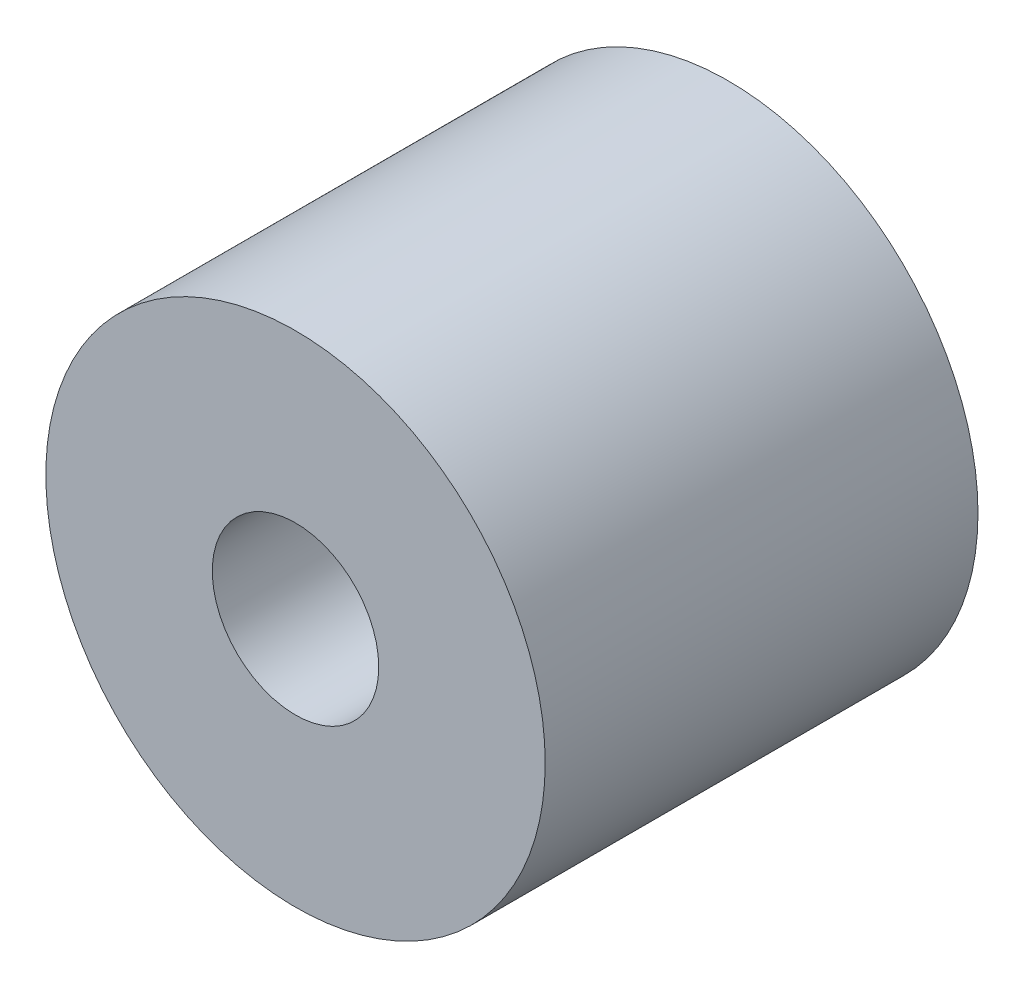
SolidWorks part; units mm, degrees
ref_plane "Front Plane" through (0, 0, 0) normal (0, 0, 1) x (1, 0, 0)
ref_plane "Top Plane" through (0, 0, 0) normal (0, 1, 0) x (1, 0, 0)
ref_plane "Right Plane" through (0, 0, 0) normal (1, 0, 0) x (0, 0, -1)
sketch "Sketch1" plane through (0, 0, 0) normal (0, 0, 1) x (1, 0, 0)
  line L0 (0, 0) -> (0, 406.0055) construction
  line L2 (0, 0) -> (-406.0055, 0) construction
  circle A0 centre (0, 0) radius 25
  circle A3 centre (0, 0) radius 75
  dimension "D1" = 150
  dimension "D3" = 50
extrude "Boss-Extrude1" add sketch "Sketch1" along normal blind 130
